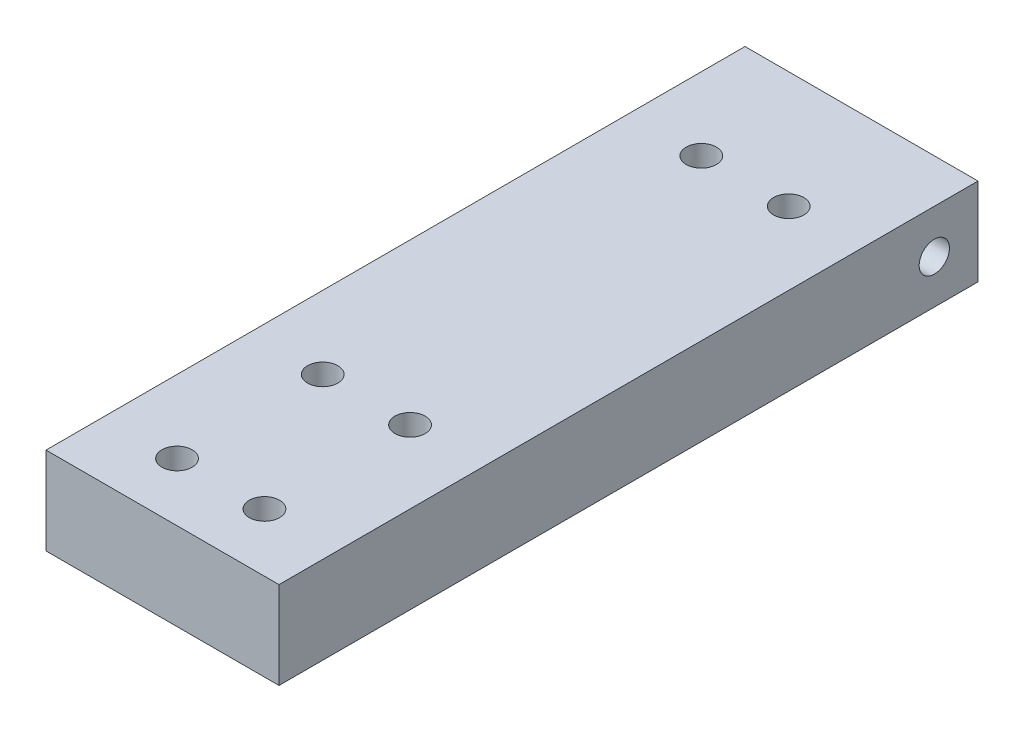
SolidWorks part; units mm, degrees
ref_plane "Front Plane" through (0, 0, 0) normal (0, 0, 1) x (1, 0, 0)
ref_plane "Top Plane" through (0, 0, 0) normal (0, 1, 0) x (1, 0, 0)
ref_plane "Right Plane" through (0, 0, 0) normal (1, 0, 0) x (0, 0, -1)
sketch "Sketch1" plane through (0, 0, 0) normal (0, 0, 1) x (1, 0, 0)
  line L1 (0, 0) -> (50.8, 0)
  line L2 (0, 0) -> (0, 19.05)
  line L3 (0, 19.05) -> (50.8, 19.05)
  line L4 (50.8, 0) -> (50.8, 19.05)
  dimension "D1" = 19.05
  dimension "D2" = 50.8
extrude "Boss-Extrude1" add sketch "Sketch1" along normal blind 152.4
hole_wizard "CBORE for M6 SHCS1" positions "Sketch3" profile "Sketch2" counterbore size "M6" standard "ANSI Metric" end condition through all
sketch "Sketch3" plane through (0, 0, 0) normal (0, -1, 0) x (-1, 0, 0)
  point P0 (-34.925, -139.7)
  point P3 (-34.925, -107.95)
  point P6 (-15.875, -107.95)
  point P9 (-15.875, -139.7)
sketch "Sketch2" plane through (34.925, 0, 139.7) normal (1, 0, 0) x (0, 0, -1)
  line L0 (0, 0) -> (0, 19.05)
  line L1 (0, 19.05) -> (3.3, 19.05)
  line L3 (3.3, 19.05) -> (3.3, 12.35)
  line L4 (3.3, 12.35) -> (5.5, 12.35)
  line L5 (5.5, 12.35) -> (5.5, 0)
  line L7 (5.5, 0) -> (0, 0)
  line L11 (0, -6.35) -> (0, 107.95) construction
  dimension "Thru Hole Dia." = 6.6
  dimension "Thru Hole Depth" = 19.05
  dimension "C'Bore Dia." = 11
  dimension "C'Bore Depth" = 12.35
hole_wizard "M6 Clearance Hole1" positions "Sketch6" profile "Sketch5" hole size "M6" standard "ANSI Metric" end condition through all
sketch "Sketch6" plane through (0, 0, 0) normal (-1, 0, 0) x (0, 0, 1)
  line L0 (0, 19.05) -> (0, 0) construction
  line L2 (0, 9.525) -> (9.525, 9.525) construction
  point P0 (9.525, 9.525)
  dimension "D1" = 9.525
sketch "Sketch5" plane through (0, 9.525, 9.525) normal (0, 1, 0) x (0, 0, 1)
  line L0 (0, 0) -> (0, 50.8)
  line L1 (0, 50.8) -> (3.3, 50.8)
  line L2 (3.3, 50.8) -> (3.3, 0)
  line L5 (3.3, 0) -> (0, 0)
  line L11 (0, -6.35) -> (0, 107.95) construction
  dimension "Thru Hole Dia." = 6.6
  dimension "Thru Hole Depth" = 50.8
hole_wizard "M6 Clearance Hole2" positions "Sketch8" profile "Sketch7" hole size "M6" standard "ANSI Metric" end condition through all
sketch "Sketch8" plane through (0, 0, 0) normal (0, -1, 0) x (-1, 0, 0)
  point P0 (-34.925, -25.4)
  point P3 (-15.875, -25.4)
sketch "Sketch7" plane through (34.925, 0, 25.4) normal (1, 0, 0) x (0, 0, -1)
  line L0 (0, 0) -> (0, 19.05)
  line L1 (0, 19.05) -> (3.3, 19.05)
  line L2 (3.3, 19.05) -> (3.3, 0)
  line L5 (3.3, 0) -> (0, 0)
  line L11 (0, -6.35) -> (0, 107.95) construction
  dimension "Thru Hole Dia." = 6.6
  dimension "Thru Hole Depth" = 19.05
